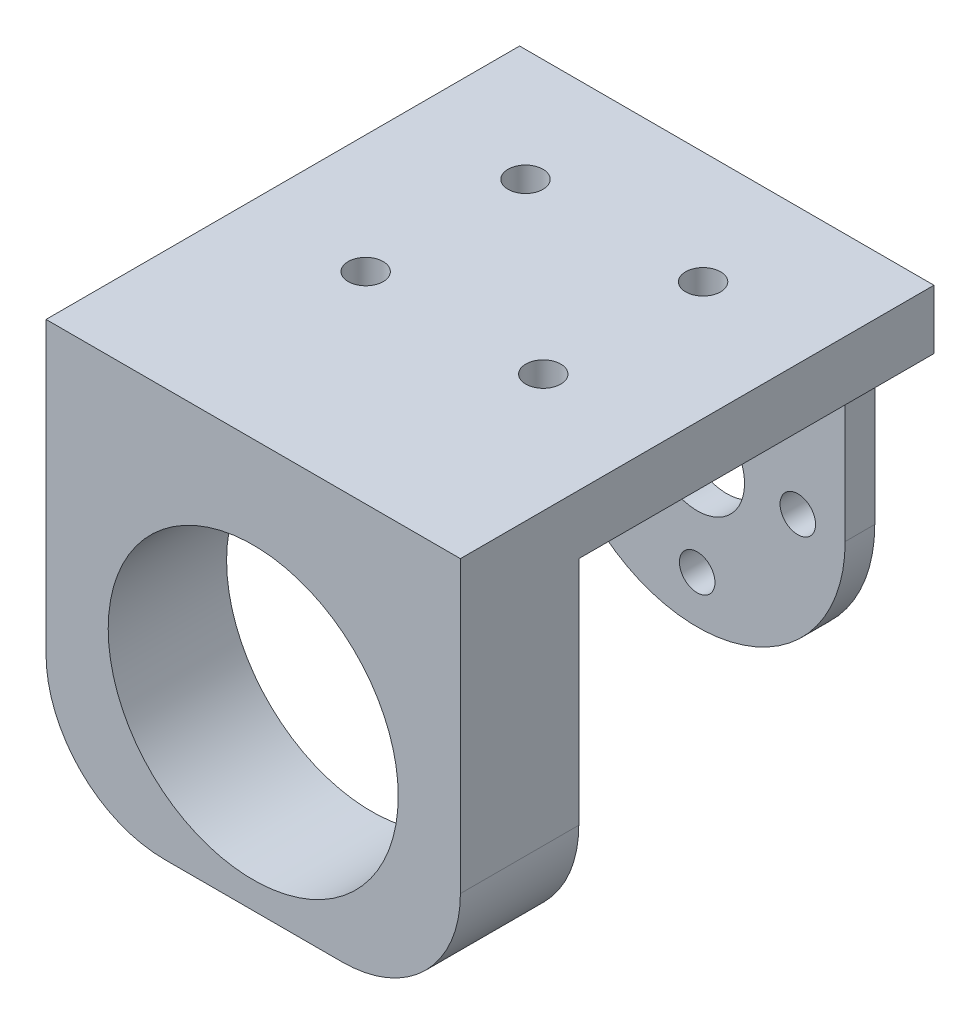
SolidWorks part; units mm, degrees
ref_plane "Front Plane" through (0, 0, 0) normal (0, 0, 1) x (1, 0, 0)
ref_plane "Top Plane" through (0, 0, 0) normal (0, 1, 0) x (1, 0, 0)
ref_plane "Right Plane" through (0, 0, 0) normal (1, 0, 0) x (0, 0, -1)
sketch "Sketch1" plane through (0, 0, 0) normal (0, 0, 1) x (1, 0, 0)
  line L1 (-12.5, 20) -> (12.5, 20)
  line L2 (-12.5, 20) -> (-12.5, -20)
  line L3 (-12.5, -20) -> (12.5, -20)
  line L4 (12.5, 20) -> (12.5, -20)
  line L5 (-12.5, 20) -> (12.5, -20) construction
  line L6 (-12.5, -20) -> (12.5, 20) construction
  circle A0 centre (0, 0) radius 12.5
  circle A1 centre (0, 0) radius 4
  point P0 (0, 0)
  dimension "D3" = 8
  dimension "D1" = 25
  dimension "D2" = 40
extrude "Boss-Extrude1" add sketch "Sketch1" along normal blind 2.5 contours A0 L4 L1 L2 | A0 A1
sketch "Sketch2" plane through (0, 0, 0) normal (0, 0, -1) x (-1, 0, 0)
  line L0 (-17.5, 15) -> (17.5, 15)
  line L1 (-12.5, -20) -> (12.5, -20)
  line L2 (-12.5, -20) -> (-12.5, 20)
  line L3 (-12.5, 20) -> (12.5, 20)
  line L4 (12.5, -20) -> (12.5, 20)
  line L5 (-12.5, -20) -> (12.5, 20) construction
  line L6 (-12.5, 20) -> (12.5, -20) construction
  line L7 (-17.5, -20) -> (17.5, -20)
  line L8 (-17.5, -20) -> (-17.5, 20)
  line L9 (-17.5, 20) -> (17.5, 20)
  line L10 (17.5, -20) -> (17.5, 20)
  line L11 (-17.5, -20) -> (17.5, 20) construction
  line L12 (-17.5, 20) -> (17.5, -20) construction
  circle A0 centre (0, 0) radius 4
  circle A1 centre (0, 0) radius 12.5
  line M9 (12.5, 0) -> (12.5, 20)
  line M10 (12.5, 20) -> (-12.5, 20)
  line M11 (-12.5, 20) -> (-12.5, 0)
  dimension "D1" = 35
  dimension "D2" = 40
  dimension "D3" = 5
extrude "Boss-Extrude3" add sketch "Sketch2" against normal blind 40 contours L0 M11 M9 M10 | L9 L8 L0 M11 | L0 L10 L9 M9
sketch "Sketch3" plane through (0, 15, 0) normal (0, -1, 0) x (1, 0, 0)
  line L0 (17.5, 40) -> (17.5, 0) construction
  line L1 (-17.5, 40) -> (17.5, 40)
  line L2 (-17.5, 40) -> (-17.5, 30)
  line L3 (-17.5, 30) -> (17.5, 30)
  line L4 (17.5, 40) -> (17.5, 30)
  dimension "D1" = 10
extrude "Boss-Extrude5" add sketch "Sketch3" along normal blind 29.5 contours L2 L1 L4 L3
sketch "Sketch5" plane through (0, 0, 30) normal (0, 0, -1) x (-1, 0, 0)
  line L1 (-17.5, 15) -> (17.5, 15)
  line L2 (-17.5, 15) -> (-17.5, -4.5)
  line L3 (-7.5, -14.5) -> (7.5, -14.5)
  line L4 (17.5, 15) -> (17.5, -4.5)
  line L5 (-17.5, 15) -> (17.5, 15)
  line L6 (-17.5, 15) -> (-17.5, -14.5)
  line L7 (-17.5, -14.5) -> (17.5, -14.5)
  line L8 (17.5, 15) -> (17.5, -14.5)
  circle A0 centre (0, 0) radius 12.25
  arc A1 (-7.5, -14.5) -> (-17.5, -4.5) centre (-7.5, -4.5) cw
  arc A2 (17.5, -4.5) -> (7.5, -14.5) centre (7.5, -4.5) cw
  point P13 (17.5, -14.5)
  line M9 (-17.5, 15) -> (-17.5, -14.5)
  line M10 (-17.5, -14.5) -> (17.5, -14.5)
  line M11 (17.5, -14.5) -> (17.5, 15)
  dimension "D1" = 24.5
  dimension "D2" = 10
extrude "Cut-Extrude1" cut sketch "Sketch5" against normal blind 29.5 contours A0 | A2 M11 M10 | A1 M10 M9
sketch "Sketch6" plane through (0, 0, 0) normal (0, 0, -1) x (-1, 0, 0)
  line L0 (0, 8.5) -> (0, -8.5)
  circle A0 centre (0, 0) radius 4
  circle A1 centre (0, 8.5) radius 1.5
  circle A2 centre (0, -8.5) radius 1.5
  point P6 (0, 0)
  dimension "D2" = 3
  dimension "D1" = 17
extrude "Cut-Extrude2" cut sketch "Sketch6" against normal blind 29.5
sketch "Sketch7" plane through (0, 15, 0) normal (0, -1, 0) x (1, 0, 0)
  line L0 (-17.5, 30) -> (-17.5, 0) construction
  line L1 (17.5, 30) -> (-17.5, 30)
  line L2 (17.5, 30) -> (17.5, 2.5)
  line L3 (17.5, 2.5) -> (-17.5, 2.5)
  line L4 (-17.5, 30) -> (-17.5, 2.5)
  line L5 (17.5, 23) -> (-17.5, 23) construction
  line L6 (17.5, 9.5) -> (-17.5, 9.5) construction
  circle A0 centre (7.5, 23) radius 1.475
  circle A1 centre (-7.5, 23) radius 1.475
  circle A2 centre (7.5, 9.5) radius 1.475
  circle A3 centre (-7.5, 9.5) radius 1.475
  point P7 (17.5, 23)
  point P8 (17.5, 9.5)
  point P11 (7.5, 23)
  point P14 (7.5, 9.5)
  point P15 (-7.5, 23)
  point P16 (-7.5, 9.5)
  dimension "D8" = 2.95
  dimension "D1" = 27.5
  dimension "D2" = 7
  dimension "D3" = 7
  dimension "D4" = 10
  dimension "D5" = 10
  dimension "D6" = 10
  dimension "D7" = 10
extrude "Cut-Extrude4" cut sketch "Sketch7" against normal blind 10 contours A0 | A2 | A3 | A1
sketch "Sketch8" plane through (0, 0, 0) normal (0, 0, -1) x (-1, 0, 0)
  line L1 (-17.5, 15) -> (17.5, 15)
  line L2 (-17.5, 15) -> (-17.5, 20)
  line L3 (-17.5, 20) -> (17.5, 20)
  line L4 (17.5, 15) -> (17.5, 20)
  circle A0 centre (0, 0) radius 4
  circle A1 centre (0, -8.5) radius 1.5
  circle A2 centre (0, 8.5) radius 1.5
  circle A3 centre (-8.5, 0) radius 1.5
  circle A4 centre (0, 8.5) radius 1.5
  circle A5 centre (8.5, 0) radius 1.5
  dimension "D1" = 4
extrude "Cut-Extrude5" cut sketch "Sketch8" against normal blind 10 contours A3 | A5
